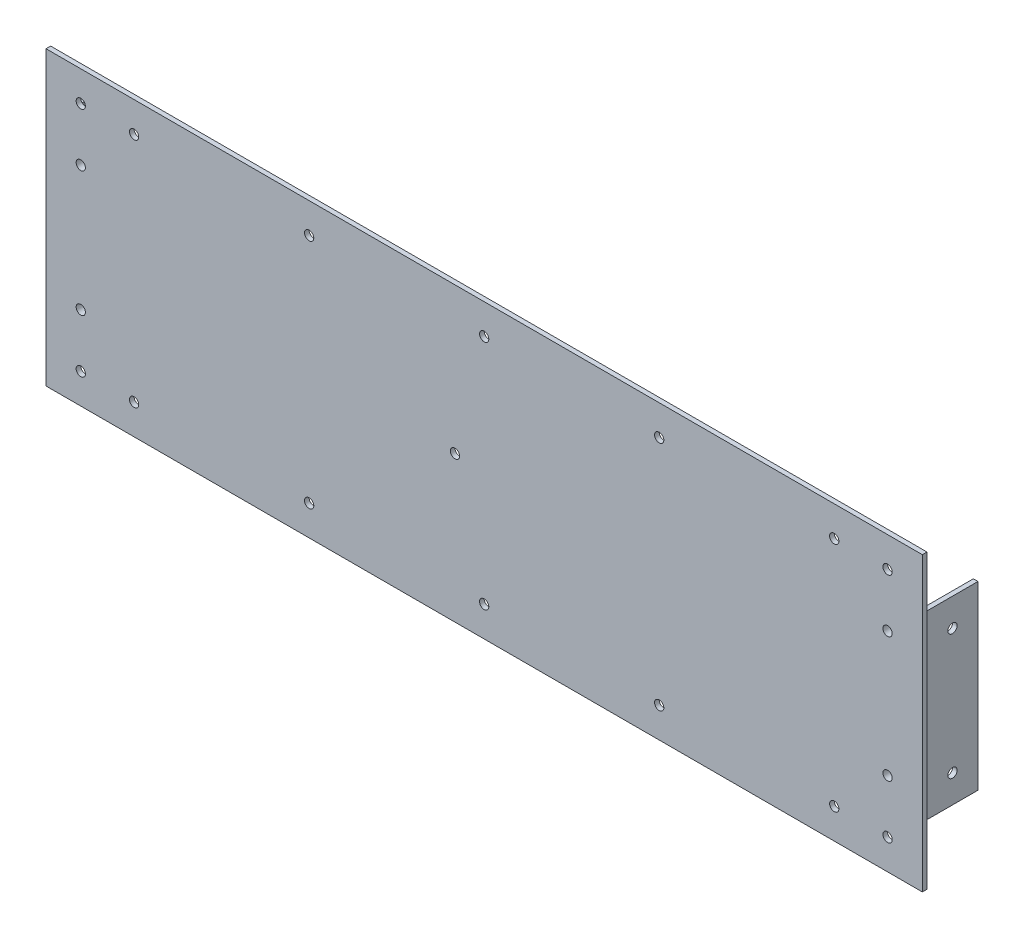
SolidWorks part; units mm, degrees
ref_plane "Plan de face" through (0, 0, 0) normal (0, 0, 1) x (1, 0, 0)
ref_plane "Plan de dessus" through (0, 0, 0) normal (0, 1, 0) x (1, 0, 0)
ref_plane "Plan de droite" through (0, 0, 0) normal (1, 0, 0) x (0, 0, -1)
sketch "Esquisse1" plane through (0, 0, 0) normal (0, 0, 1) x (1, 0, 0)
  line L1 (-120.1017, 81.1475) -> (179.8983, 81.1475)
  line L2 (-120.1017, 81.1475) -> (-120.1017, -18.8525)
  line L3 (-120.1017, -18.8525) -> (179.8983, -18.8525)
  line L4 (179.8983, 81.1475) -> (179.8983, -18.8525)
  dimension "D1" = 300
  dimension "D2" = 100
extrude "Boss.-Extru.1" add sketch "Esquisse1" along normal blind 1.5875
sketch "Esquisse2" plane through (0, 0, 0) normal (0, 0, -1) x (-1, 0, 0)
  line L1 (99.4642, 62.0975) -> (118.5142, 62.0975)
  line L2 (99.4642, 62.0975) -> (99.4642, 0.1975)
  line L3 (99.4642, 0.1975) -> (118.5142, 0.1975)
  line L4 (118.5142, 62.0975) -> (118.5142, 0.1975)
  line L5 (-178.3108, 62.0975) -> (-159.2608, 62.0975)
  line L6 (-178.3108, 62.0975) -> (-178.3108, 0.1975)
  line L7 (-178.3108, 0.1975) -> (-159.2608, 0.1975)
  line L8 (-159.2608, 62.0975) -> (-159.2608, 0.1975)
  line L10 (-179.8983, 81.1475) -> (120.1017, 81.1475) construction
  line L11 (-159.2608, 62.0975) -> (-159.2608, 81.1475) construction
  line L12 (-159.2608, 0.1975) -> (-159.2608, -18.8525) construction
  line L13 (120.1017, -18.8525) -> (-179.8983, -18.8525) construction
  line L14 (120.1017, 81.1475) -> (120.1017, -18.8525) construction
  line L15 (-179.8983, -18.8525) -> (-179.8983, 81.1475) construction
  point P8 (-176.1577, 0.1975)
  point P10 (118.6434, 0.1975)
  point P11 (117.0972, 62.0975)
  point P14 (101.0517, 0.1975)
  dimension "D1" = 19.05
  dimension "D2" = 19.05
  dimension "D3" = 1.5875
  dimension "D4" = 1.5875
extrude "Boss.-Extru.2" add sketch "Esquisse2" along normal blind 1.5875
sketch "Esquisse3" plane through (0, 0, -1.5875) normal (0, 0, -1) x (-1, 0, 0)
  line L0 (118.5142, 0.1975) -> (118.5142, 62.0975) construction
  line L1 (-178.3108, 62.0975) -> (-176.7233, 62.0975)
  line L2 (-178.3108, 62.0975) -> (-178.3108, 0.1975)
  line L3 (-178.3108, 0.1975) -> (-176.7233, 0.1975)
  line L4 (-176.7233, 62.0975) -> (-176.7233, 0.1975)
  line L5 (116.9267, 62.0975) -> (118.5142, 62.0975)
  line L6 (116.9267, 62.0975) -> (116.9267, 0.1975)
  line L7 (116.9267, 0.1975) -> (118.5142, 0.1975)
  line L8 (118.5142, 62.0975) -> (118.5142, 0.1975)
  line L9 (118.5142, 62.0975) -> (99.4642, 62.0975) construction
  line L10 (99.4642, 0.1975) -> (118.5142, 0.1975) construction
  line L11 (-178.3108, 62.0975) -> (-178.3108, 0.1975) construction
  line L12 (-159.2608, 62.0975) -> (-178.3108, 62.0975) construction
  line L13 (-178.3108, 0.1975) -> (-159.2608, 0.1975) construction
  dimension "D1" = 1.5875
extrude "Boss.-Extru.3" add sketch "Esquisse3" along normal blind 17.4625
sketch "Esquisse4" plane through (0, 0, -1.5875) normal (0, 0, -1) x (-1, 0, 0)
  line L0 (-176.7233, 14.7337) -> (-159.2608, 14.7337) construction
  line L1 (-176.7233, 0.1975) -> (-176.7233, 62.0975) construction
  line L2 (-159.2608, 0.1975) -> (-159.2608, 62.0975) construction
  line L3 (99.4642, 15.3602) -> (116.9267, 15.3602) construction
  line L4 (99.4642, 62.0975) -> (99.4642, 0.1975) construction
  line L5 (116.9267, 62.0975) -> (116.9267, 0.1975) construction
  line L6 (-167.9921, 52.5725) -> (-167.9921, 9.7225) construction
  line L7 (-159.2608, 62.0975) -> (-176.7233, 62.0975) construction
  circle A0 centre (-167.9921, 52.5725) radius 1.5875
  circle A1 centre (-167.9921, 9.7225) radius 1.5875
  circle A2 centre (108.1954, 52.5725) radius 1.5875
  circle A3 centre (108.1954, 9.7225) radius 1.5875
  point P8 (108.1954, 15.3602)
  point P9 (-167.9921, 14.7337)
  point P22 (-167.9921, 31.1475)
  point P23 (-176.7233, 31.1475)
  dimension "D1" = 3.175
  dimension "D2" = 9.525
extrude "Enlèv. mat.-Extru.1" cut sketch "Esquisse4" against normal up to next
sketch "Esquisse5" plane through (0, 0, 1.5875) normal (0, 0, 1) x (1, 0, 0)
  line L0 (-120.1017, -18.8525) -> (179.8983, -18.8525) construction
  line L1 (-120.1017, 81.1475) -> (-120.1017, -18.8525) construction
  line L2 (179.8983, -18.8525) -> (179.8983, 81.1475) construction
  line L3 (-30.0204, -8.5337) -> (89.8171, -8.5337) construction
  line L4 (-120.1017, 31.1475) -> (179.8983, 31.1475) construction
  line L5 (-99.4642, 62.0975) -> (-99.4642, 0.1975) construction
  line L6 (159.2608, 0.1975) -> (159.2608, 62.0975) construction
  line L7 (149.7358, -8.5337) -> (29.8983, -8.5337) construction
  circle A0 centre (-108.1954, -8.5337) radius 1.5875
  circle A1 centre (-89.9392, -8.5337) radius 1.5875
  circle A2 centre (-30.0204, -8.5337) radius 1.5875
  circle A3 centre (29.8983, -8.5337) radius 1.5875
  circle A4 centre (89.8171, -8.5337) radius 1.5875
  circle A5 centre (149.7358, -8.5337) radius 1.5875
  circle A6 centre (167.9921, -8.5337) radius 1.5875
  circle A7 centre (167.9921, 70.8288) radius 1.5875
  circle A8 centre (149.7358, 70.8288) radius 1.5875
  circle A9 centre (89.8171, 70.8288) radius 1.5875
  circle A10 centre (29.8983, 70.8288) radius 1.5875
  circle A11 centre (-30.0204, 70.8288) radius 1.5875
  circle A12 centre (-89.9392, 70.8288) radius 1.5875
  circle A13 centre (-108.1954, 70.8288) radius 1.5875
  circle A14 centre (167.9921, 9.7225) radius 1.5875 construction
  circle A15 centre (167.9921, 9.7225) radius 1.5875 construction
  circle A16 centre (-108.1954, 9.7225) radius 1.5875 construction
  circle A17 centre (-108.1954, 9.7225) radius 1.5875 construction
  point P14 (29.8983, -8.5337)
  point P22 (29.8983, -18.8525)
  point P41 (89.8171, -8.5337)
  dimension "D1" = 3.175
  dimension "D2" = 10.3187
  dimension "D3" = 9.525
  dimension "D4" = 9.525
extrude "Enlèv. mat.-Extru.2" cut sketch "Esquisse5" against normal up to next
sketch "Esquisse6" plane through (0, 0, 1.5875) normal (0, 0, 1) x (1, 0, 0)
  line L0 (-120.1017, 81.1475) -> (-120.1017, -18.8525) construction
  circle A0 centre (19.8983, 31.1475) radius 1.5875
  point P2 (0, 0)
  point P5 (-120.1017, 31.1475)
  dimension "D1" = 3.175
  dimension "D2" = 140
extrude "Enlèv. mat.-Extru.3" cut sketch "Esquisse6" against normal up to next
sketch "Esquisse7" plane through (176.7233, 0, 0) normal (-1, 0, 0) x (0, 0, 1)
  line L0 (-1.5875, 54.16) -> (-1.5875, 50.985) construction
  line L1 (-1.5875, 11.31) -> (-1.5875, 8.135) construction
  line L2 (-1.5875, 54.16) -> (-1.5875, 50.985) construction
  line L3 (-1.5875, 11.31) -> (-1.5875, 8.135) construction
  line L4 (-19.05, 16.0041) -> (-1.5875, 16.0041) construction
  line L5 (-19.05, 0.1975) -> (-19.05, 62.0975) construction
  line L6 (-1.5875, 0.1975) -> (-1.5875, 62.0975) construction
  circle A0 centre (-10.3187, 52.5725) radius 1.5875
  circle A1 centre (-10.3187, 9.7225) radius 1.5875
  point P8 (0, 0)
  point P9 (-1.5875, 52.5725)
  point P10 (-1.5875, 9.7225)
  point P17 (-10.3187, 16.0041)
  dimension "D1" = 3.175
extrude "Enlèv. mat.-Extru.4" cut sketch "Esquisse7" against normal through all both and the other way through all
